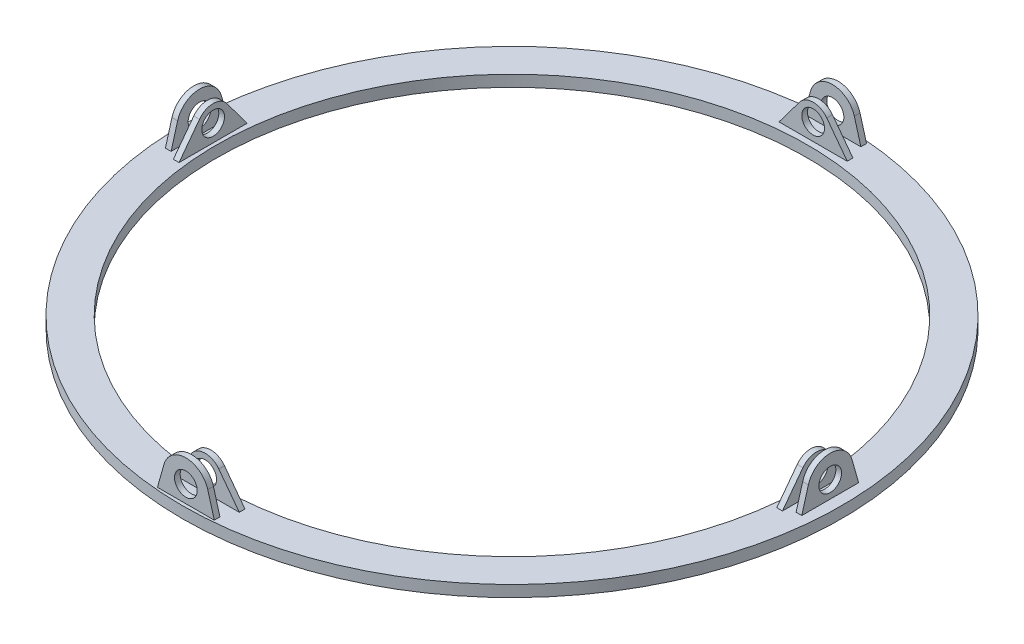
SolidWorks part; units mm, degrees
ref_plane "Front Plane" through (0, 0, 0) normal (0, 0, 1) x (1, 0, 0)
ref_plane "Top Plane" through (0, 0, 0) normal (0, 1, 0) x (1, 0, 0)
ref_plane "Right Plane" through (0, 0, 0) normal (1, 0, 0) x (0, 0, -1)
sketch "Sketch1" plane through (0, 0, 0) normal (0, 1, 0) x (1, 0, 0)
  circle A0 centre (0, 0) radius 145
  circle A1 centre (0, 0) radius 130
  dimension "D1" = 290
  dimension "D2" = 260
extrude "Boss-Extrude1" add sketch "Sketch1" along normal blind 5
sketch "Sketch4" plane through (0, 5, 0) normal (0, 1, 0) x (1, 0, 0)
  line L0 (0, 145) -> (0, -145) construction
  circle A0 centre (0, 0) radius 145 construction
ref_plane "Plane1" through (0, 0, 145) normal (0, 0, 1) x (1, 0, 0)
sketch "Sketch5" plane through (0, 0, 145) normal (0, 0, 1) x (1, 0, 0)
  line L0 (0, 5) -> (0, 12.5) construction
  line L1 (145, 5) -> (-145, 5) construction
  line L2 (-15, 5) -> (15, 5)
  line L3 (-15, 5) -> (-6, 17)
  line L4 (15, 5) -> (6, 17)
  arc A0 (6, 17) -> (-6, 17) centre (0, 12.5) ccw
  circle A1 centre (0, 12.5) radius 5
  point P9 (0, 5)
  dimension "D2" = 10
  dimension "D4" = 7.5
  dimension "D1" = 7.5
  dimension "D3" = 30
extrude "Boss-Extrude2" add sketch "Sketch5" against normal blind 2.5 from offset 10 offset against normal yes
sketch "Sketch6" plane through (0, 0, 145) normal (0, 0, 1) x (1, 0, 0)
  line L0 (0, 5) -> (0, 12.5) construction
  line L1 (145, 5) -> (-145, 5) construction
  line L2 (-12.5, 5) -> (12.5, 5)
  line L3 (-12.5, 5) -> (-9.6259, 15.2098)
  line L4 (12.5, 5) -> (9.6259, 15.2098)
  circle A0 centre (0, 12.5) radius 5
  arc A1 (9.6259, 15.2098) -> (-9.6259, 15.2098) centre (0, 12.5) ccw
  point P9 (0, 5)
  dimension "D2" = 10
  dimension "D3" = 20
  dimension "D1" = 7.5
  dimension "D4" = 25
extrude "Boss-Extrude3" add sketch "Sketch6" against normal blind 2.5 from offset 1.5 separate body offset against normal yes
mirror "Mirror1" about plane through (0, 0, 0) normal (0, 0, 1) of "Boss-Extrude3", "Boss-Extrude2"
sketch "Sketch8" plane through (0, 0, 0) normal (1, 0, 0) x (0, 0, -1)
  line L0 (0, 5) -> (0, 12.5) construction
  line L1 (130, 5) -> (-130, 5) construction
  line L2 (-12.5, 5) -> (12.5, 5)
  line L3 (145, 5) -> (-145, 5) construction
  line L4 (-12.5, 5) -> (-9.6259, 15.2098)
  line L5 (12.5, 5) -> (9.6259, 15.2098)
  circle A0 centre (0, 12.5) radius 5
  arc A1 (9.6259, 15.2098) -> (-9.6259, 15.2098) centre (0, 12.5) ccw
  point P11 (0, 5)
  dimension "D3" = 10
  dimension "D4" = 20
  dimension "D1" = 7.5
  dimension "D2" = 25
extrude "Boss-Extrude4" add sketch "Sketch8" along normal blind 2.5 from offset 137.5
sketch "Sketch10" plane through (0, 0, 0) normal (1, 0, 0) x (0, 0, -1)
  line L0 (0, 5) -> (0, 12.5) construction
  line L1 (145, 5) -> (-145, 5) construction
  line L2 (-15, 5) -> (15, 5)
  line L3 (130, 5) -> (-130, 5) construction
  line L4 (-15, 5) -> (-6, 17)
  line L5 (15, 5) -> (6, 17)
  circle A0 centre (0, 12.5) radius 5
  arc A1 (6, 17) -> (-6, 17) centre (0, 12.5) ccw
  point P11 (0, 5)
  dimension "D2" = 10
  dimension "D3" = 15
  dimension "D1" = 30
extrude "Boss-Extrude5" add sketch "Sketch10" along normal blind 2.5 from offset 131.5
mirror "Mirror2" about plane through (0, 0, 0) normal (1, 0, 0) of "Boss-Extrude4", "Boss-Extrude5"
